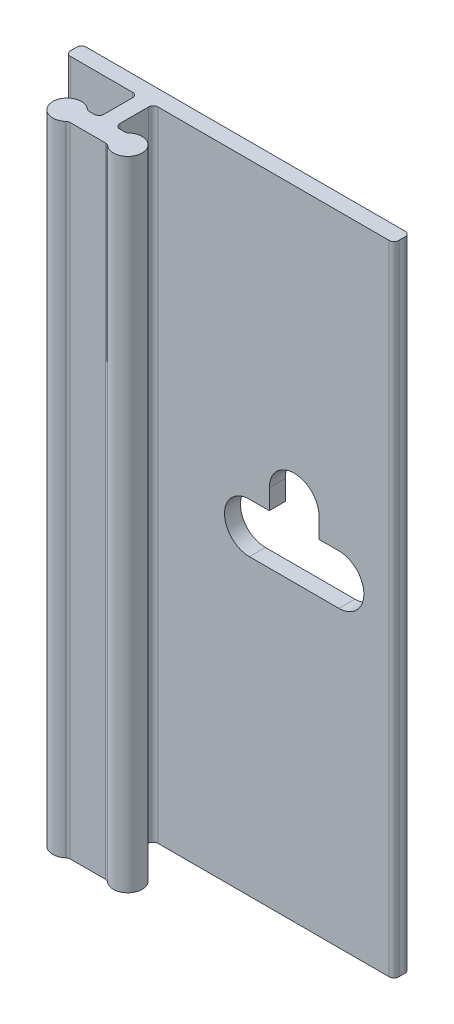
SolidWorks part; units mm, degrees
ref_plane "Front Plane" through (0, 0, 0) normal (0, 0, 1) x (1, 0, 0)
ref_plane "Top Plane" through (0, 0, 0) normal (0, 1, 0) x (1, 0, 0)
ref_plane "Right Plane" through (0, 0, 0) normal (1, 0, 0) x (0, 0, -1)
sketch "Sketch2" plane through (0, 0, 0) normal (0, 1, 0) x (1, 0, 0)
  line L0 (0, 7.209) -> (0, -15.6826) construction
  line L16 (-5.969, 0) -> (19.431, 0)
  line L18 (19.812, -0.381) -> (19.812, -0.889)
  line L19 (19.431, -1.27) -> (1.016, -1.27)
  line L20 (0.635, -1.651) -> (0.635, -3.937)
  line L52 (-0.635, -1.651) -> (-0.635, -3.937)
  line L53 (-8.0148, -5.08) -> (8.0148, -5.08) construction
  line L54 (-1.405, -4.318) -> (-1.016, -4.318)
  line L55 (-1.405, -5.842) -> (1.405, -5.842)
  line L56 (1.016, -4.318) -> (1.405, -4.318)
  line L57 (-1.016, -1.27) -> (-5.969, -1.27)
  line L58 (-6.35, -0.889) -> (-6.35, -0.381)
  arc A11 (19.431, 0) -> (19.812, -0.381) centre (19.431, -0.381) cw
  arc A12 (19.812, -0.889) -> (19.431, -1.27) centre (19.431, -0.889) cw
  arc A19 (1.016, -1.27) -> (0.635, -1.651) centre (1.016, -1.651) ccw
  arc A20 (-1.657, -4.2227) -> (-1.657, -5.9373) centre (-2.413, -5.08) ccw
  arc A21 (1.657, -5.9373) -> (1.657, -4.2227) centre (2.413, -5.08) ccw
  arc A22 (0.635, -3.937) -> (1.016, -4.318) centre (1.016, -3.937) ccw
  arc A23 (-0.635, -3.937) -> (-1.016, -4.318) centre (-1.016, -3.937) cw
  arc A24 (1.405, -5.842) -> (1.657, -5.9373) centre (1.405, -6.223) cw
  arc A25 (1.657, -4.2227) -> (1.405, -4.318) centre (1.405, -3.937) cw
  arc A26 (-1.405, -5.842) -> (-1.657, -5.9373) centre (-1.405, -6.223) ccw
  arc A27 (-1.405, -4.318) -> (-1.657, -4.2227) centre (-1.405, -3.937) cw
  arc A28 (-6.35, -0.381) -> (-5.969, 0) centre (-5.969, -0.381) cw
  arc A29 (-5.969, -1.27) -> (-6.35, -0.889) centre (-5.969, -0.889) cw
  arc A30 (-1.016, -1.27) -> (-0.635, -1.651) centre (-1.016, -1.651) cw
  point P7 (0, -5.08)
  point P16 (19.812, 0)
  point P19 (19.812, -1.27)
  point P22 (0.635, -1.27)
  point P30 (0.635, -4.318)
  point P36 (1.5611, -5.842)
  point P39 (1.5611, -4.318)
  point P42 (-1.5611, -5.842)
  point P45 (-1.5611, -4.318)
  dimension "D7" = 0.381
  dimension "D6" = 2.286
  dimension "D10" = 1.524
  dimension "D11" = 19.812
  dimension "D12" = 6.35
  dimension "D2" = 1.27
  dimension "D3" = 1.27
  dimension "D4" = 0.635
  dimension "D5" = 5.08
  dimension "D8" = 2.413
  dimension "D9" = 2.413
extrude "Boss-Extrude1" add sketch "Sketch2" along normal blind 50.8
sketch "Sketch3" plane through (0, 0, 1.27) normal (0, 0, 1) x (1, 0, 0)
  line L0 (8.2931, 25.4) -> (15.4305, 25.4) construction
  line L1 (8.2931, 27.3812) -> (9.8806, 27.3812)
  line L2 (8.2931, 23.4188) -> (15.4305, 23.4188)
  line L3 (19.812, 50.8) -> (19.812, 0) construction
  line L4 (13.843, 28.9814) -> (13.843, 27.3812)
  line L5 (9.8806, 28.9814) -> (9.8806, 27.3812)
  line L6 (13.843, 27.3812) -> (15.4305, 27.3812)
  line L7 (1.016, 0) -> (19.431, 0) construction
  arc A0 (8.2931, 27.3812) -> (8.2931, 23.4188) centre (8.2931, 25.4) ccw
  arc A1 (15.4305, 23.4188) -> (15.4305, 27.3812) centre (15.4305, 25.4) ccw
  arc A2 (13.843, 28.9814) -> (9.8806, 28.9814) centre (11.8618, 28.9814) ccw
  point P2 (11.8618, 25.4)
  dimension "D2" = 1.9812
  dimension "D3" = 3.5814
  dimension "D1" = 7.1374
  dimension "D4" = 7.9502
  dimension "D5" = 25.4
extrude "Cut-Extrude1" cut sketch "Sketch3" against normal through all
pattern_linear "LPattern1" [suppressed] count 2 spacing 203.2
